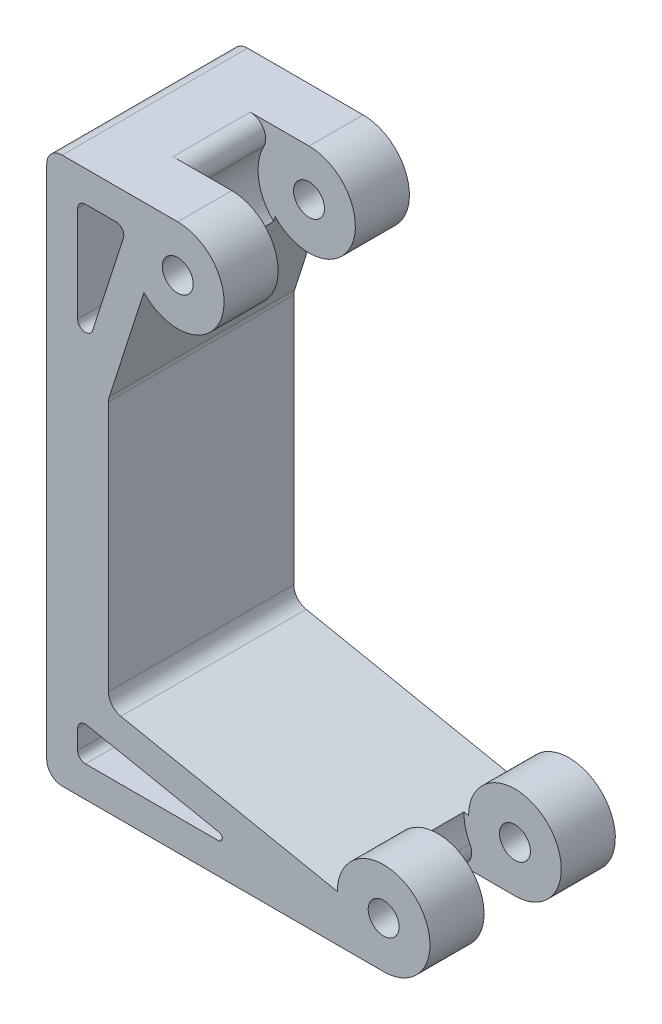
SolidWorks part; units mm, degrees
ref_plane "Front Plane" through (0, 0, 0) normal (0, 0, 1) x (1, 0, 0)
ref_plane "Top Plane" through (0, 0, 0) normal (0, 1, 0) x (1, 0, 0)
ref_plane "Right Plane" through (0, 0, 0) normal (1, 0, 0) x (0, 0, -1)
sketch "Sketch1" plane through (0, 0, 0) normal (0, 0, 1) x (1, 0, 0)
  line L0 (0, 0) -> (21.8174, 0)
  line L2 (0, 0) -> (0, 35.3819)
  line L3 (0, 35.3819) -> (8.4836, 35.3819)
  line L5 (6.2976, 30.3272) -> (4, 23.2001)
  line L6 (4, 23.2001) -> (4, 5.9735)
  line L7 (4, 5.9735) -> (18.8174, 3)
  line L11 (8.4836, 32.3819) -> (21.8174, 3) construction
  line L12 (5.181, 33.3819) -> (2, 33.3819)
  line L13 (2, 33.3819) -> (2, 23.5145)
  line L14 (2, 23.5145) -> (5.181, 33.3819)
  line L15 (8.4836, 32.3819) -> (8.4836, 5.1119) construction
  line L16 (8.4836, 5.1119) -> (21.8174, 3) construction
  line L17 (8.4836, 5.1119) -> (8.4836, -11.812) construction
  line L18 (2, 2) -> (2, 4.335)
  line L19 (2, 4.335) -> (13.6355, 2)
  line L20 (13.6355, 2) -> (2, 2)
  arc A0 (21.8174, 0) -> (18.8174, 3) centre (21.8174, 3) ccw
  arc A1 (8.4836, 35.3819) -> (6.2976, 30.3272) centre (8.4836, 32.3819) cw
  circle A2 centre (8.4836, 32.3819) radius 1
  circle A3 centre (21.8174, 3) radius 1
  point P16 (11.6021, 3)
  point P18 (7.1852, 29.8349)
  point P19 (6.7371, 31.1191)
  point P22 (6.9346, 33.3819)
  point P23 (7.4549, 33.3819)
  point P26 (6.6898, 31.6658)
  point P27 (7.3293, 35.3819)
  point P28 (6.3501, 30.4901)
  point P29 (0, 0)
  point P30 (18.8174, 3)
  dimension "D1" = 2
  dimension "D3" = 3
  dimension "D2" = 4
  dimension "D6" = 2
  dimension "D4" = 27.27
  dimension "D5" = 13.5
  dimension "D8" = 81
  dimension "D9" = 2
  dimension "D10" = 2
  dimension "D11" = 2
  dimension "D7" = 2
extrude "Boss-Extrude1" add sketch "Sketch1" along normal blind 12
ref_plane "midplane" through (0, 0, 6) normal (0, 0, 1) x (1, 0, 0)
sketch "Sketch2" plane through (0, 0, 6) normal (0, 0, 1) x (1, 0, 0)
  circle A0 centre (8.4836, 32.3819) radius 3.3
  circle A1 centre (21.8174, 3) radius 3.3
  dimension "D1" = 6.6
extrude "Cut-Extrude1" cut sketch "Sketch2" against normal blind 2.5 and the other way blind 2.5
fillet "Fillet1" radius 1 2 edges at (0, 0, 6) (0, 35.3819, 6)
fillet "Fillet2" radius 1 2 edges at (4, 5.9735, 6) (4, 23.2001, 6)
fillet "Fillet3" radius 1 2 edges at (7.1088, 35.3819, 6) (20.4426, 0, 6)
fillet "Fillet4" radius 0.5 5 edges at (2, 23.5145, 6) (5.181, 33.3819, 6) (2, 33.3819, 6) (2, 2, 6) (2, 4.335, 6)
fillet "Fillet5" radius 0.25 1 edges at (13.6355, 2, 6)
equation "\"axle-diameter\"=2"
equation "\"D1@Sketch1\"=\"axle-diameter\""
equation "\"switch-thickness\"=12"
equation "\"D1@Boss-Extrude1\"=\"switch-thickness\""
equation "\"base-width\"=4.0"
equation "\"D2@Sketch1\"=\"base-width\""
equation "\"axle-bushing-radius\"=3"
equation "\"D3@Sketch1\"= \"axle-bushing-radius\""
equation "\"D1@Sketch2\"=\"axle-bushing-radius\"*2.2"
equation "\"D1@Cut-Extrude1\"=\"switch-thickness\"/6+\"clearance\""
equation "\"D2@Cut-Extrude1\"=\"switch-thickness\"/6+\"clearance\""
equation "\"clearance\"= 0.5"
equation "\"arm-width\"=3.0"
